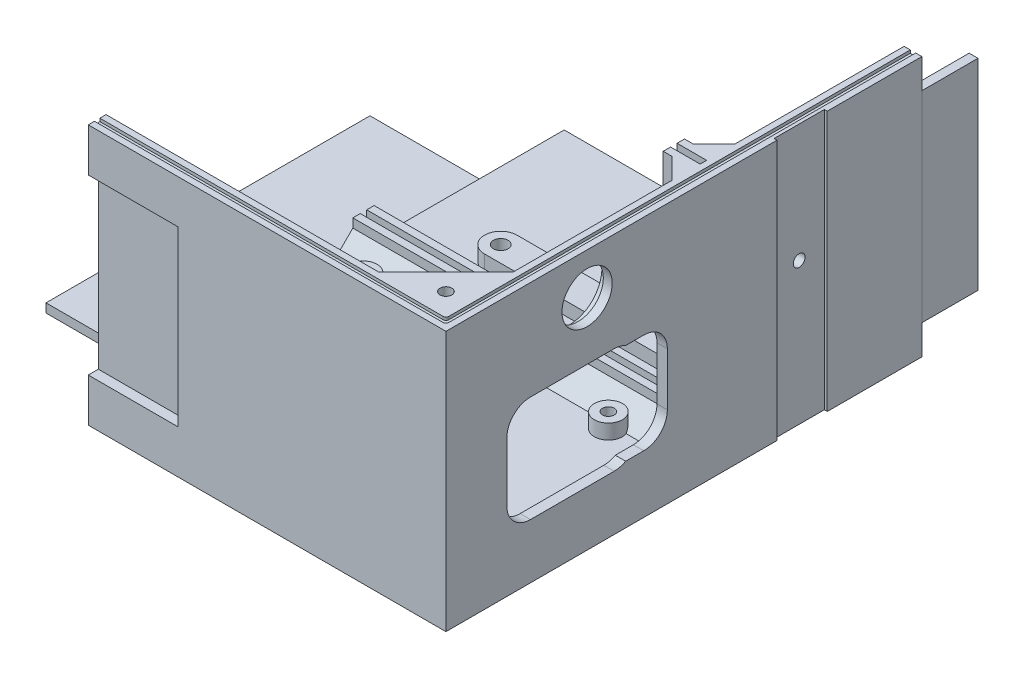
SolidWorks part; units mm, degrees
ref_plane "Front Plane" through (0, 0, 0) normal (0, 0, 1) x (1, 0, 0)
ref_plane "Top Plane" through (0, 0, 0) normal (0, 1, 0) x (1, 0, 0)
ref_plane "Right Plane" through (0, 0, 0) normal (1, 0, 0) x (0, 0, -1)
sketch "Sketch1" plane through (0, 0, 0) normal (0, 1, 0) x (1, 0, 0)
  line L1 (0, 0) -> (121, 0)
  line L2 (0, 0) -> (0, -161)
  line L3 (0, -161) -> (121, -161)
  line L4 (121, 0) -> (121, -161)
  dimension "D1" = 161
  dimension "D2" = 121
extrude "Boss-Extrude1" add sketch "Sketch1" along normal blind 88
sketch "Sketch2" plane through (0, 88, 0) normal (0, 1, 0) x (1, 0, 0)
  line L0 (121, -161) -> (121, 0) construction
  line L1 (0, 0) -> (115, 0)
  line L2 (0, 0) -> (0, -155)
  line L3 (0, -155) -> (115, -155)
  line L4 (115, 0) -> (115, -155)
  line L5 (0, -161) -> (121, -161) construction
  dimension "D1" = 6
  dimension "D2" = 6
extrude "Cut-Extrude1" cut sketch "Sketch2" against normal blind 82
sketch "Sketch3" plane through (0, 0, 0) normal (0, -1, 0) x (1, 0, 0)
  line L0 (121, 0) -> (0, 0) construction
  line L1 (24.7, 0) -> (96.3, 0)
  line L2 (24.7, 0) -> (24.7, 10)
  line L3 (24.7, 10) -> (96.3, 10)
  line L4 (96.3, 0) -> (96.3, 10)
  line L5 (0, 0) -> (0, 161) construction
  line L6 (121, 161) -> (121, 0) construction
  dimension "D1" = 24.7
  dimension "D2" = 24.7
  dimension "D3" = 10
extrude "Cut-Extrude2" cut sketch "Sketch3" against normal blind 3.4
sketch "Sketch5" plane through (0, 0, 0) normal (0, -1, 0) x (1, 0, 0)
  line L0 (0, 0) -> (0, 161) construction
  line L1 (0, 135.3) -> (-40, 135.3)
  line L2 (0, 135.3) -> (0, 25.7)
  line L3 (0, 25.7) -> (-40, 25.7)
  line L4 (-40, 135.3) -> (-40, 25.7)
  line L5 (0, 161) -> (121, 161) construction
  line L6 (24.7, 0) -> (0, 0) construction
  dimension "D1" = 25.7
  dimension "D2" = 25.7
  dimension "D3" = 40
extrude "Boss-Extrude2" add sketch "Sketch5" against normal blind 3
sketch "Sketch6" plane through (0, 0, 161) normal (0, 0, 1) x (1, 0, 0)
  line L0 (0, 88) -> (0, 0) construction
  line L1 (0, 73.3) -> (30.4, 73.3)
  line L2 (0, 73.3) -> (0, 14.7)
  line L3 (0, 14.7) -> (30.4, 14.7)
  line L4 (30.4, 73.3) -> (30.4, 14.7)
  line L5 (0, 0) -> (121, 0) construction
  line L6 (0, 88) -> (121, 88) construction
  dimension "D1" = 14.7
  dimension "D2" = 14.7
  dimension "D3" = 30.4
extrude "Cut-Extrude3" cut sketch "Sketch6" against normal blind 3.4
sketch "Sketch7" plane through (121, 0, 0) normal (1, 0, 0) x (0, 0, -1)
  line L0 (0, 88) -> (0, 0) construction
  line L1 (0, 78) -> (19, 78)
  line L2 (0, 78) -> (0, 10)
  line L3 (0, 10) -> (19, 10)
  line L4 (19, 78) -> (19, 10)
  line L5 (-161, 0) -> (0, 0) construction
  line L6 (-161, 88) -> (0, 88) construction
  dimension "D1" = 10
  dimension "D2" = 10
  dimension "D3" = 19
extrude "Boss-Extrude3" add sketch "Sketch7" against normal blind 3 separate body
sketch "Sketch8" plane through (121, 0, 0) normal (1, 0, 0) x (0, 0, -1)
  line L2 (-155, 6) -> (-155, 88) construction
  line L3 (-155, 88) -> (0, 88) construction
  circle A1 centre (-113.25, 74) radius 8.5
  dimension "D1" = 17
  dimension "D2" = 41.75
  dimension "D3" = 14
extrude "Cut-Extrude4" cut sketch "Sketch8" against normal through all
sketch "Sketch9" plane through (115, 0, 0) normal (-1, 0, 0) x (0, 0, 1)
  line L0 (155, 88) -> (0, 88) construction
  line L1 (71.5, 88) -> (69, 88)
  line L2 (71.5, 88) -> (71.5, 6)
  line L3 (71.5, 6) -> (69, 6)
  line L4 (69, 88) -> (69, 6)
  line L5 (155, 6) -> (0, 6) construction
  line L7 (66.8, 88) -> (64.3, 88)
  line L8 (66.8, 88) -> (66.8, 6)
  line L9 (66.8, 6) -> (64.3, 6)
  line L10 (64.3, 88) -> (64.3, 6)
  line L11 (155, 6) -> (155, 88) construction
  dimension "D1" = 2.5
  dimension "D2" = 2.5
  dimension "D3" = 2.2
  dimension "D4" = 83.5
extrude "Boss-Extrude4" add sketch "Sketch9" along normal blind 10
sketch "Sketch10" plane through (0, 6, 0) normal (0, 1, 0) x (1, 0, 0)
  line L0 (0, 0) -> (0, -155) construction
  line L1 (105, -66.8) -> (0, -66.8)
  line L2 (105, -66.8) -> (105, -64.3)
  line L3 (105, -64.3) -> (0, -64.3)
  line L4 (0, -66.8) -> (0, -64.3)
  line L6 (105, -71.5) -> (0, -71.5)
  line L7 (105, -71.5) -> (105, -69)
  line L8 (105, -69) -> (0, -69)
  line L9 (0, -71.5) -> (0, -69)
  dimension "D1" = 2.5
  dimension "D2" = 2.5
extrude "Boss-Extrude5" add sketch "Sketch10" along normal blind 10
sketch "Sketch11" plane through (0, 88, 0) normal (0, 1, 0) x (1, 0, 0)
  line L0 (115, -155) -> (92.3726, -155)
  line L1 (0, -155) -> (115, -155) construction
  line L2 (92.3726, -155) -> (115, -132.3726)
  line L3 (115, -155) -> (115, -71.5) construction
  line L4 (115, -132.3726) -> (115, -155)
  line L5 (115, -155) -> (103.6863, -143.6863) construction
  dimension "D2" = 16
extrude "Boss-Extrude6" add sketch "Sketch11" against normal blind 9
sketch "Sketch12" plane through (0, 88, 0) normal (0, 1, 0) x (1, 0, 0)
  line L0 (115, -132.3726) -> (115, -155) construction
  line L1 (115, -155) -> (92.3726, -155) construction
  line L2 (103.6863, -143.6863) -> (115, -155) construction
  line L3 (115, -132.3726) -> (92.3726, -155) construction
  circle A0 centre (109.3431, -149.3431) radius 2
  dimension "D1" = 4
extrude "Cut-Extrude6" cut sketch "Sketch12" against normal blind 5
sketch "Sketch13" plane through (0, 6, 0) normal (0, 1, 0) x (1, 0, 0)
  line L0 (115, -155) -> (115, -148)
  line L1 (115, -155) -> (115, -71.5) construction
  line L2 (115, -148) -> (108, -155)
  line L3 (0, -155) -> (115, -155) construction
  line L4 (108, -155) -> (115, -155)
  dimension "D1" = 7
extrude "Boss-Extrude7" add sketch "Sketch13" along normal up to surface (73 mm away) up to face at (107.4575, 79, 147.4575)
sketch "Sketch14" plane through (0, 6, 0) normal (0, 1, 0) x (1, 0, 0)
  line L0 (27.4746, -71.5) -> (27.4746, -155) construction
  line L1 (40.53, -80.05) -> (95, -80.05) construction
  line L2 (40.53, -80.05) -> (40.53, -146.45) construction
  line L3 (40.53, -146.45) -> (95, -146.45) construction
  line L4 (95, -80.05) -> (95, -146.45) construction
  line L5 (67.765, -146.45) -> (67.765, -80.05) construction
  line L6 (40.53, -113.25) -> (95, -113.25) construction
  line L7 (0, -71.5) -> (115, -71.5) construction
  line L8 (0, -155) -> (108, -155) construction
  line L9 (115, -148) -> (115, -71.5) construction
  circle A0 centre (40.53, -80.05) radius 4.75
  circle A1 centre (95, -80.05) radius 4.75
  circle A2 centre (40.53, -146.45) radius 4.75
  circle A3 centre (95, -146.45) radius 4.75
  point P0 (67.765, -113.25)
  point P4 (27.4746, -113.25)
  dimension "D4" = 9.5
  dimension "D1" = 66.4
  dimension "D2" = 54.47
  dimension "D3" = 20
extrude "Boss-Extrude8" add sketch "Sketch14" along normal blind 5
sketch "Sketch15" plane through (0, 11, 0) normal (0, 1, 0) x (1, 0, 0)
  circle A0 centre (40.53, -80.05) radius 2
  circle A1 centre (95, -80.05) radius 2
  circle A2 centre (40.53, -146.45) radius 2
  circle A3 centre (95, -146.45) radius 2
  dimension "D1" = 4
  dimension "D2" = 4
extrude "Cut-Extrude7" cut sketch "Sketch15" against normal blind 5
sketch "Sketch16" plane through (0, 6, 0) normal (0, 1, 0) x (1, 0, 0)
  line L0 (105, -64.3) -> (0, -64.3) construction
  line L1 (115, -64.3) -> (115, 0) construction
  line L2 (27.85, -43.8) -> (88, -43.8)
  line L3 (27.85, -54.8) -> (88, -54.8)
  circle A0 centre (85, -28.3) radius 4.75
  arc A1 (88, -54.8) -> (88, -43.8) centre (88, -49.3) ccw
  arc A2 (27.85, -43.8) -> (27.85, -54.8) centre (27.85, -49.3) ccw
  dimension "D5" = 11
  dimension "D6" = 9.5
  dimension "D1" = 15
  dimension "D2" = 36
  dimension "D3" = 30
  dimension "D4" = 27
  dimension "D7" = 60.15
extrude "Boss-Extrude9" add sketch "Sketch16" along normal blind 5
sketch "Sketch17" plane through (0, 11, 0) normal (0, 1, 0) x (1, 0, 0)
  circle A1 centre (85, -28.3) radius 2
  dimension "D2" = 4
extrude "Cut-Extrude8" cut sketch "Sketch17" against normal blind 5
sketch "Sketch18" plane through (0, 11, 0) normal (0, 1, 0) x (1, 0, 0)
  circle A0 centre (88, -49.3) radius 2.5
  circle A1 centre (27.85, -49.3) radius 2.5
  dimension "D1" = 5
extrude "Cut-Extrude9" cut sketch "Sketch18" against normal blind 6
sketch "Sketch19" plane through (0, 6, 0) normal (0, 1, 0) x (1, 0, 0)
  line L0 (115, -71.5) -> (108, -71.5)
  line L1 (0, -71.5) -> (115, -71.5) construction
  line L2 (108, -71.5) -> (115, -78.5)
  line L3 (115, -148) -> (115, -71.5) construction
  line L4 (115, -78.5) -> (115, -71.5)
  line L5 (115, -64.3) -> (115, -57.3)
  line L6 (115, -64.3) -> (115, 0) construction
  line L7 (115, -57.3) -> (108, -64.3)
  line L8 (0, -64.3) -> (115, -64.3) construction
  line L9 (108, -64.3) -> (115, -64.3)
  dimension "D1" = 7
  dimension "D2" = 7
  dimension "D3" = 7
  dimension "D4" = 7
extrude "Boss-Extrude10" add sketch "Sketch19" along normal up to surface (82 mm away) up to face at (109.3431, 88, 151.3431)
sketch "Sketch20" plane through (0, 6, 0) normal (0, 1, 0) x (1, 0, 0)
  line L0 (0, -71.5) -> (108, -71.5) construction
  line L1 (0, -71.5) -> (0, -155) construction
  circle A0 centre (12.71, -80.76) radius 4.75
  circle A1 centre (12.71, -141.75) radius 4.75
  circle A2 centre (12.71, -80.76) radius 2
  circle A3 centre (12.71, -141.75) radius 2
  dimension "D1" = 4
  dimension "D2" = 9.5
  dimension "D3" = 9.26
  dimension "D4" = 60.99
  dimension "D5" = 12.71
extrude "Boss-Extrude11" add sketch "Sketch20" along normal blind 5
sketch "Sketch21" plane through (0, 0, 0) normal (-1, 0, 0) x (0, 0, 1)
  line L0 (71.5, 6) -> (71.5, 13)
  line L1 (71.5, 16) -> (71.5, 6) construction
  line L2 (71.5, 13) -> (78.5, 6)
  line L3 (71.5, 6) -> (155, 6) construction
  line L4 (78.5, 6) -> (71.5, 6)
  dimension "D1" = 7
  dimension "D2" = 7
extrude "Boss-Extrude12" add sketch "Sketch21" against normal up to surface (115 mm away)
sketch "Sketch22" plane through (0, 0, 0) normal (-1, 0, 0) x (0, 0, 1)
  line L0 (57.3, 6) -> (64.3, 13)
  line L1 (0, 6) -> (64.3, 6) construction
  line L2 (64.3, 16) -> (64.3, 6) construction
  line L3 (64.3, 13) -> (64.3, 6)
  line L4 (64.3, 6) -> (57.3, 6)
  dimension "D1" = 7
  dimension "D2" = 7
extrude "Boss-Extrude13" add sketch "Sketch22" against normal up to surface (108 mm away)
sketch "Sketch23" plane through (0, 0, 0) normal (0, 0, -1) x (-1, 0, 0)
  line L0 (-115, 6) -> (-115, 13)
  line L1 (-115, 6) -> (-115, 88) construction
  line L2 (-115, 13) -> (-108, 6)
  line L3 (-115, 6) -> (0, 6) construction
  line L4 (-108, 6) -> (-115, 6)
  dimension "D1" = 7
  dimension "D2" = 7
extrude "Boss-Extrude14" add sketch "Sketch23" against normal up to surface (57.3 mm away)
sketch "Sketch25" plane through (0, 0, 161) normal (0, 0, 1) x (1, 0, 0)
  line L0 (121, 0) -> (115, 0) construction
  line L1 (0, 0) -> (121, 0) construction
  line L2 (115, 0) -> (115, 6) construction
  line L3 (115, 6) -> (115, 13)
  line L4 (115, 13) -> (108, 6)
  line L5 (108, 6) -> (115, 6)
  dimension "D1" = 6
  dimension "D2" = 6
  dimension "D3" = 7
  dimension "D4" = 7
extrude "Boss-Extrude15" add sketch "Sketch25" against normal up to surface (82.5 mm away)
sketch "Sketch26" plane through (0, 0, 0) normal (-1, 0, 0) x (0, 0, 1)
  line L0 (155, 6) -> (148, 6)
  line L1 (78.5, 6) -> (155, 6) construction
  line L2 (148, 6) -> (155, 13)
  line L3 (155, 6) -> (155, 88) construction
  line L4 (155, 13) -> (155, 6)
  dimension "D1" = 7
  dimension "D2" = 7
extrude "Boss-Extrude16" add sketch "Sketch26" against normal up to surface (108 mm away)
sketch "Sketch27" plane through (0, 6, 0) normal (0, 1, 0) x (1, 0, 0)
  line L0 (80.2769, -28.8051) -> (82.5312, -49.8848)
  line L1 (89.6756, -27.4624) -> (93.4138, -48.3302)
  circle A0 centre (85, -28.3) radius 4.75 construction
  circle A1 centre (88, -49.3) radius 5.5 construction
  arc A2 (80.2769, -28.8051) -> (89.6756, -27.4624) centre (85, -28.3) ccw
  arc A3 (93.4138, -48.3302) -> (82.5312, -49.8848) centre (88, -49.3) ccw
extrude "Boss-Extrude17" add sketch "Sketch27" along normal blind 5
sketch "Sketch28" plane through (0, 88, 0) normal (0, 1, 0) x (1, 0, 0)
  line L0 (0, -157.1) -> (0, -158.9)
  line L1 (0, -155) -> (0, -161) construction
  line L2 (0, -158.9) -> (118.9, -158.9)
  line L3 (118.9, -158.9) -> (118.9, 0)
  line L4 (118.9, 0) -> (117.1, 0)
  line L5 (117.1, 0) -> (117.1, -157.1)
  line L6 (117.1, -157.1) -> (0, -157.1)
  line L7 (121, 0) -> (115, 0) construction
  point P4 (0, -158)
  point P9 (0, -158)
  point P10 (118, 0)
  point P13 (118, 0)
  dimension "D1" = 1.8
  dimension "D2" = 1.8
extrude "Cut-Extrude10" cut sketch "Sketch28" against normal blind 1
sketch "Sketch29" plane through (115, 0, 0) normal (-1, 0, 0) x (0, 0, 1)
  circle A0 centre (113.25, 74) radius 11
  dimension "D1" = 22
extrude "Cut-Extrude11" cut sketch "Sketch29" against normal blind 3
sketch "Sketch30" plane through (121, 0, 0) normal (1, 0, 0) x (0, 0, -1)
  line L0 (-161, 88) -> (0, 88) construction
  line L1 (-60, 88) -> (-30, 88)
  line L2 (-60, 88) -> (-60, 78)
  line L3 (-60, 78) -> (-30, 78)
  line L4 (-30, 88) -> (-30, 78)
  line L5 (0, 88) -> (0, 0) construction
  dimension "D1" = 30
  dimension "D2" = 10
  dimension "D3" = 30
extrude "Boss-Extrude18" [suppressed] add sketch "Sketch30" along normal blind 30
chamfer "Chamfer1" [suppressed] distance 10 distance2 15
sketch "Sketch31" plane through (115, 0, 0) normal (-1, 0, 0) x (0, 0, 1)
  line L0 (148, 79) -> (148, 13) construction
  line L1 (78.5, 13) -> (148, 13)
  line L2 (78.5, 13) -> (78.5, 60)
  line L3 (78.5, 60) -> (148, 60)
  line L4 (148, 13) -> (148, 60)
  dimension "D1" = 47
extrude "Cut-Extrude12" cut sketch "Sketch31" against normal blind 2.5
sketch "Sketch32" plane through (117.5, 0, 0) normal (-1, 0, 0) x (0, 0, 1)
  line L0 (113.25, 60) -> (113.25, 13) construction
  line L1 (148, 60) -> (78.5, 60) construction
  line L2 (78.5, 13) -> (148, 13) construction
  line L3 (78.5, 36.5) -> (148, 36.5) construction
  line L4 (78.5, 60) -> (78.5, 13) construction
  line L5 (148, 13) -> (148, 60) construction
  line L6 (86.1, 45.45) -> (86.1, 27.55)
  line L7 (140.4, 46.45) -> (140.4, 26.55)
  line L8 (78.5, 54.45) -> (100.2, 54.45) construction
  line L9 (104.073, 18.55) -> (132.4, 18.55)
  line L10 (94.1, 53.45) -> (100.2, 53.45)
  line L11 (100.2, 60) -> (100.2, 19.55) construction
  line L12 (94.1, 19.55) -> (100.2, 19.55)
  line L14 (104.073, 54.45) -> (132.4, 54.45)
  arc A0 (94.1, 19.55) -> (86.1, 27.55) centre (94.1, 27.55) cw
  arc A1 (140.4, 26.55) -> (132.4, 18.55) centre (132.4, 26.55) cw
  arc A2 (140.4, 46.45) -> (132.4, 54.45) centre (132.4, 46.45) ccw
  arc A3 (94.1, 53.45) -> (86.1, 45.45) centre (94.1, 45.45) ccw
  arc A4 (104.073, 54.45) -> (100.2, 53.45) centre (104.073, 46.45) ccw
  arc A5 (100.2, 19.55) -> (104.073, 18.55) centre (104.073, 26.55) ccw
  point P32 (100.2, 19.55)
  point P33 (100.2, 53.45)
  dimension "D8" = 8
  dimension "D9" = 16
  dimension "D10" = 16
  dimension "D1" = 54.3
  dimension "D2" = 35.9
  dimension "D3" = 33.9
  dimension "D4" = 13.05
  dimension "D5" = 27.15
  dimension "D6" = 17.95
  dimension "D7" = 16.95
extrude "Cut-Extrude13" cut sketch "Sketch32" against normal up to surface (3.5 mm away) up to face at (121, 74, 104.75)
sketch "Sketch33" plane through (121, 0, 0) normal (1, 0, 0) x (0, 0, -1)
  line L0 (-161, 88) -> (0, 88) construction
  line L1 (-49, 88) -> (-32, 88)
  line L2 (-49, 88) -> (-49, 0)
  line L3 (-49, 0) -> (-32, 0)
  line L4 (-32, 88) -> (-32, 0)
  line L5 (-161, 0) -> (0, 0) construction
  line L6 (-161, 88) -> (-161, 0) construction
  dimension "D1" = 17
  dimension "D2" = 112
extrude "Cut-Extrude14" cut sketch "Sketch33" against normal blind 1
ref_plane "Plane1" through (25, 0, 0) normal (-1, 0, 0) x (0, 0, 1)
sketch "Sketch34" plane through (25, 0, 0) normal (-1, 0, 0) x (0, 0, 1)
  line L0 (133, 6) -> (148, 6)
  line L1 (78.5, 6) -> (148, 6) construction
  line L2 (148, 6) -> (155, 13)
  line L3 (155, 13) -> (155, 28)
  line L4 (155, 13) -> (155, 88) construction
  line L5 (155, 28) -> (133, 6)
  dimension "D1" = 15
  dimension "D2" = 15
extrude "Boss-Extrude19" add sketch "Sketch34" against normal blind 2
fillet "Fillet1" radius 1 1 edges at (117.1, 87.5, 157.1)
fillet "Fillet2" radius 1 1 edges at (118.9, 87.5, 158.9)
sketch "Sketch35" plane through (120, 0, 0) normal (1, 0, 0) x (0, 0, -1)
  line L0 (-32, 88) -> (-49, 88) construction
  line L1 (0, 88) -> (-156.1, 88) construction
  circle A0 centre (-40.5, 48) radius 2
  point P4 (-40.5, 88)
  dimension "D1" = 4
  dimension "D2" = 40
extrude "Cut-Extrude15" cut sketch "Sketch35" against normal blind 5
sketch "Sketch36" plane through (115, 0, 0) normal (-1, 0, 0) x (0, 0, 1)
  line L0 (49, 88) -> (49, 0) construction
  line L1 (32, 0) -> (32, 88) construction
  line L2 (49, 58) -> (49, 13)
  line L3 (32, 13) -> (32, 58)
  line L4 (32, 13) -> (49, 13)
  line L5 (57.3, 13) -> (0, 13) construction
  line L6 (32, 58) -> (49, 58)
  line L7 (57.3, 88) -> (0, 88) construction
  dimension "D1" = 30
extrude "Boss-Extrude20" add sketch "Sketch36" along normal blind 1
